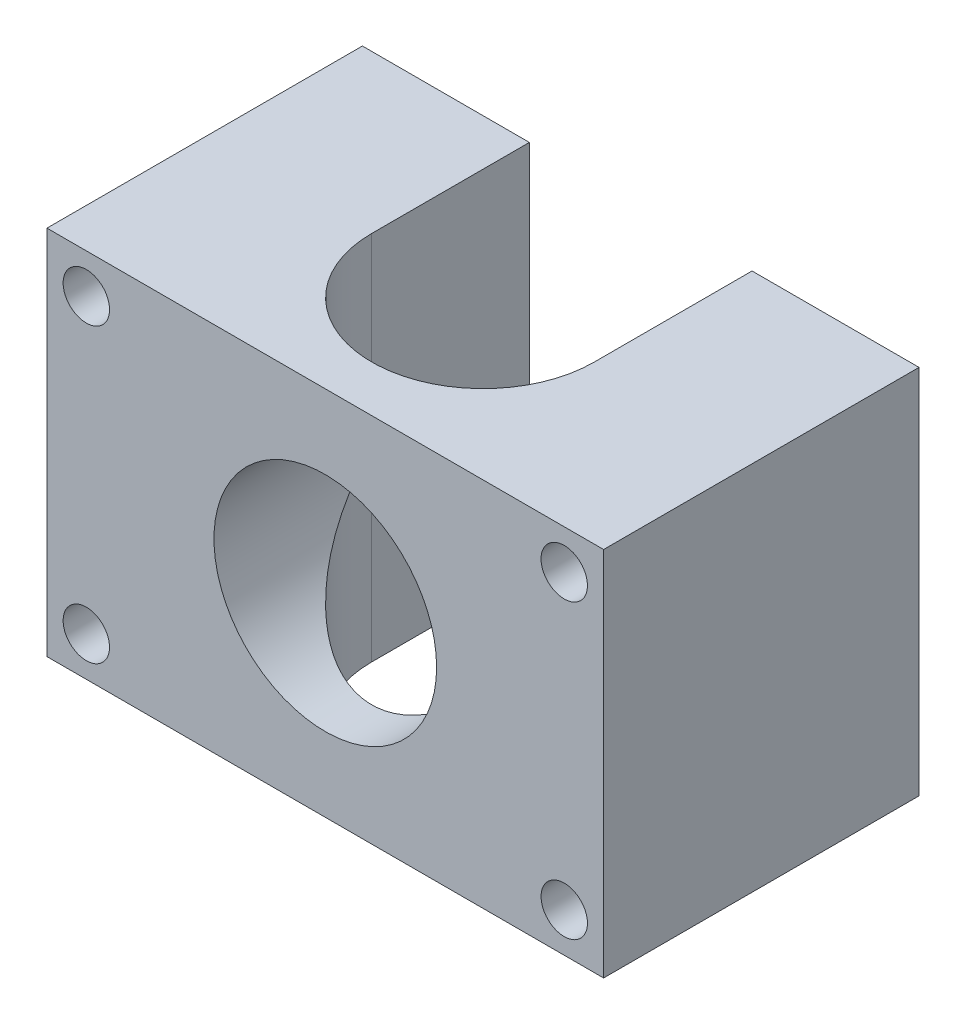
SolidWorks part; units mm, degrees
ref_plane "Front Plane" through (0, 0, 0) normal (0, 0, 1) x (1, 0, 0)
ref_plane "Top Plane" through (0, 0, 0) normal (0, 1, 0) x (1, 0, 0)
ref_plane "Right Plane" through (0, 0, 0) normal (1, 0, 0) x (0, 0, -1)
sketch "Sketch1" plane through (0, 0, 0) normal (0, 0, 1) x (1, 0, 0)
  line L1 (0, 0) -> (60, 0)
  line L2 (0, 0) -> (0, 40)
  line L3 (0, 40) -> (60, 40)
  line L4 (60, 0) -> (60, 40)
  dimension "D1" = 60
  dimension "D2" = 40
extrude "Boss-Extrude1" add sketch "Sketch1" along normal blind 34
sketch "Sketch2" plane through (0, 0, 0) normal (0, -1, 0) x (1, 0, 0)
  line L0 (30, 0) -> (30, 17) construction
  line L1 (0, 0) -> (60, 0) construction
  line L2 (42, 17) -> (42, 0)
  line L3 (18, 17) -> (18, 0)
  line L4 (18, 0) -> (42, 0)
  circle A0 centre (30, 17) radius 12
extrude "Cut-Extrude1" cut sketch "Sketch2" against normal blind 40
sketch "Sketch3" plane through (0, 0, 34) normal (0, 0, 1) x (1, 0, 0)
  line L0 (30, 0) -> (30, 20) construction
  line L1 (0, 0) -> (60, 0) construction
  circle A0 centre (30, 20) radius 12
extrude "Cut-Extrude2" cut sketch "Sketch3" against normal blind 40
sketch "Sketch4" plane through (0, 0, 34) normal (0, 0, 1) x (1, 0, 0)
  line L0 (60, 0) -> (55.7574, 4.2426) construction
  line L1 (60, 20) -> (0, 20) construction
  line L2 (60, 0) -> (60, 40) construction
  line L3 (0, 40) -> (0, 0) construction
  line L4 (30, 0) -> (30, 40) construction
  line L5 (0, 0) -> (60, 0) construction
  line L6 (60, 40) -> (0, 40) construction
  circle A0 centre (55.7574, 4.2426) radius 2.5
  circle A1 centre (4.2426, 4.2426) radius 2.5
  circle A2 centre (55.7574, 35.7574) radius 2.5
  circle A3 centre (4.2426, 35.7574) radius 2.5
extrude "Cut-Extrude3" cut sketch "Sketch4" against normal blind 40 contours A1 | A3 | A0 | A2
